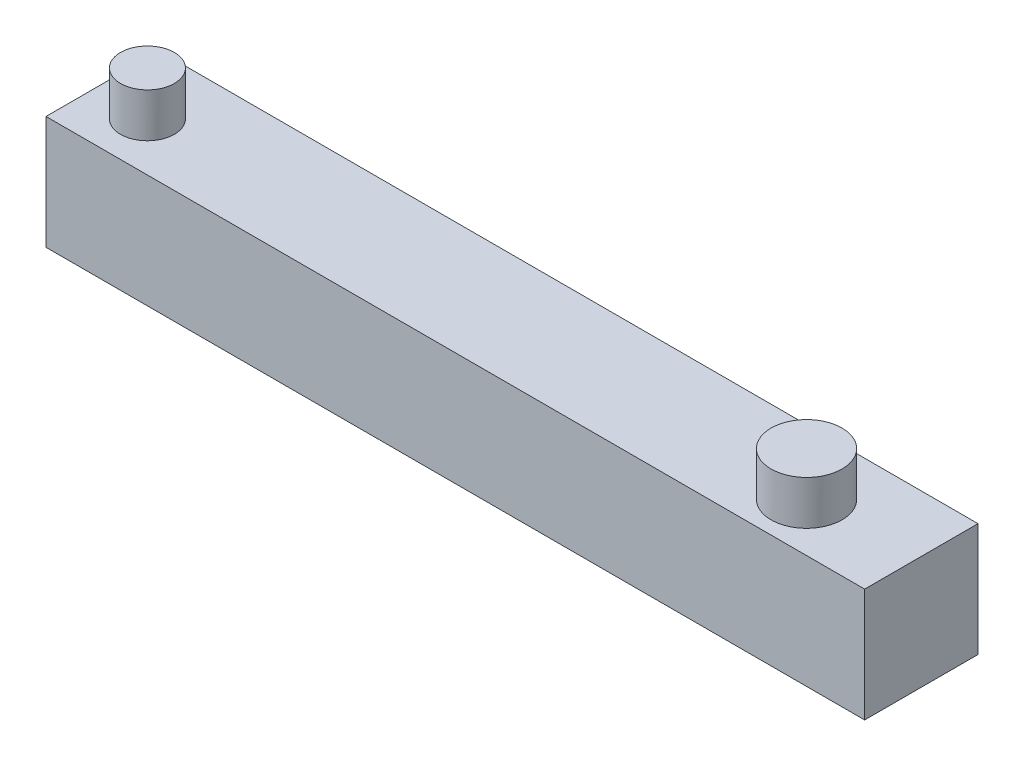
SolidWorks part; units mm, degrees
ref_plane "Front Plane" through (0, 0, 0) normal (0, 0, 1) x (1, 0, 0)
ref_plane "Top Plane" through (0, 0, 0) normal (0, 1, 0) x (1, 0, 0)
ref_plane "Right Plane" through (0, 0, 0) normal (1, 0, 0) x (0, 0, -1)
sketch "Sketch1" plane through (0, 0, 0) normal (0, 0, 1) x (1, 0, 0)
  line L1 (0, 0) -> (65, 0)
  line L2 (0, 0) -> (0, 9)
  line L3 (0, 9) -> (65, 9)
  line L4 (65, 0) -> (65, 9)
  dimension "D1" = 65
  dimension "D2" = 9
extrude "Boss-Extrude1" add sketch "Sketch1" along normal blind 9
sketch "Sketch2" plane through (0, 9, 0) normal (0, 1, 0) x (1, 0, 0)
  circle A0 centre (4.1909, -5.1381) radius 2.1358
  circle A1 centre (56.5268, -5.1381) radius 2.8165
extrude "Boss-Extrude2" add sketch "Sketch2" along normal blind 3.5
